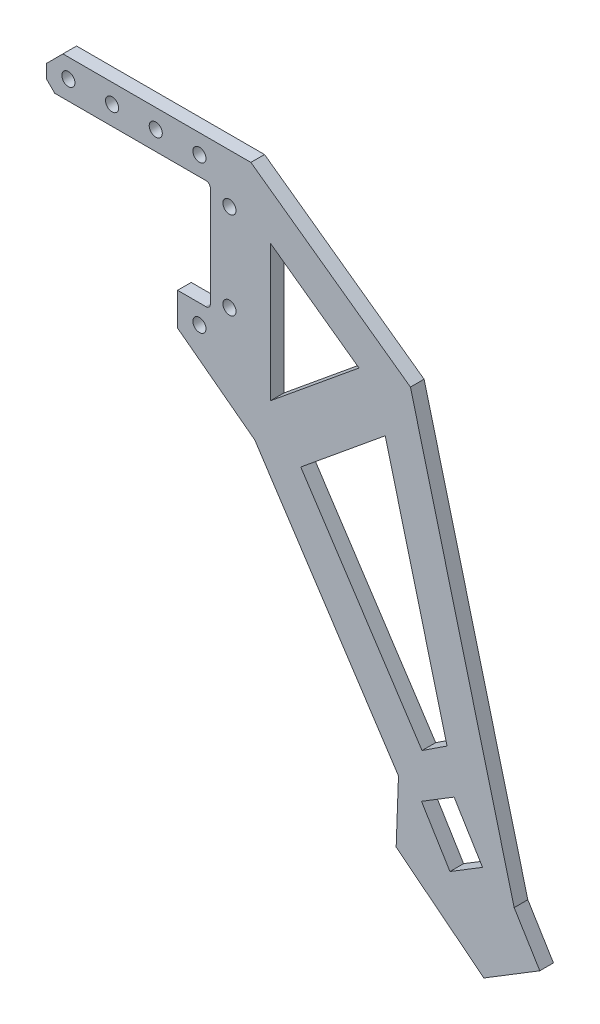
SolidWorks part; units mm, degrees
ref_plane "Plan de face" through (0, 0, 0) normal (0, 0, 1) x (1, 0, 0)
ref_plane "Plan de dessus" through (0, 0, 0) normal (0, 1, 0) x (1, 0, 0)
ref_plane "Plan de droite" through (0, 0, 0) normal (1, 0, 0) x (0, 0, -1)
sketch "Esquisse1" plane through (0, 0, 0) normal (0, 0, 1) x (1, 0, 0)
  line L0 (-12.25, 10) -> (12.25, 10)
  line L1 (19.6775, 17) -> (48.9006, -4.024)
  line L2 (48.9006, -4.024) -> (67.9013, -77.094)
  line L3 (67.9013, -77.094) -> (72.5958, -84.7726)
  line L4 (72.5958, -84.7726) -> (62.3576, -91.032)
  line L5 (62.3576, -91.032) -> (46.2854, -78.3067)
  line L6 (46.2854, -78.3067) -> (46.7112, -66.8067)
  line L7 (46.7112, -66.8067) -> (20.3918, -26.6658)
  line L8 (-12.25, 10) -> (-12.25, -10)
  line L9 (-12.25, -10) -> (12.25, -10)
  line L10 (12.25, 10) -> (12.25, -10)
  line L11 (-17.75, 10) -> (-17.75, -10)
  line L12 (-12.25, 10) -> (12.25, -10) construction
  line L13 (12.25, 10) -> (-12.25, -10) construction
  line L14 (-17.75, 10) -> (-17.75, 17)
  line L15 (-12.25, -10) -> (-17.75, -10)
  line L16 (-12.25, 10) -> (-17.75, 10)
  line L17 (44.278, -14.0621) -> (55.6029, -57.6137)
  line L18 (55.6029, -57.6137) -> (51.0231, -60.6166)
  line L19 (51.0231, -60.6166) -> (28.8161, -26.7478)
  line L20 (28.8161, -26.7478) -> (44.278, -14.0621)
  line L21 (23.25, 5.9738) -> (23.25, -19.0262)
  line L22 (23.25, -19.0262) -> (39.4851, -5.7062)
  line L23 (39.4851, -5.7062) -> (23.25, 5.9738)
  line L24 (19.6775, 17) -> (20.3918, -26.6658)
  line L25 (-1000, 0) -> (49000, 0) construction
  line L26 (-17.75, 17) -> (12.25, 17)
  line L27 (12.25, 17) -> (12.25, 10)
  line L28 (12.25, -10) -> (12.25, -16)
  line L29 (12.25, -16) -> (-17.75, -16)
  line L30 (-17.75, -16) -> (-17.75, -10)
  line L31 (19.6775, 17) -> (12.25, 17)
  line L32 (6.25, -10) -> (6.25, -16)
  line L33 (6.25, -16) -> (20.3918, -26.6658)
  point P17 (10.25, -13.5)
  point P18 (2.25, -13.5)
  point P25 (-5.75, -13.5)
  point P26 (-13.75, -13.5)
  point P27 (10.25, 13.5)
  point P28 (2.25, 13.5)
  point P29 (-5.75, 13.5)
  point P30 (-13.75, 13.5)
  point P31 (15.75, -8)
  point P32 (15.75, 8)
  dimension "D2" = 75.5
  dimension "D3" = 36
  dimension "D4" = 9
  dimension "D5" = 12
  dimension "D6" = 20.5
  dimension "D7" = 11.5
  dimension "D8" = 48
  dimension "D9" = 7
  dimension "D10" = 7
  dimension "D11" = 9.5
  dimension "D12" = 20
  dimension "D13" = 24.5
  dimension "D14" = 8
  dimension "D15" = 27
  dimension "D16" = 3.5
  dimension "D17" = 2
  dimension "D18" = 3.5
  dimension "D19" = 2
  dimension "D20" = 5.5
  dimension "D21" = 8
  dimension "D22" = 8
  dimension "D23" = 8
  dimension "D24" = 8
  dimension "D25" = 8
  dimension "D26" = 16
  dimension "D27" = 6
  dimension "D28" = 7
  dimension "D29" = 4
  dimension "D30" = 11
  dimension "D31" = 20
  dimension "D32" = 40.5
  dimension "D33" = 45
  dimension "D34" = 20
  dimension "D35" = 21
  dimension "D36" = 25
extrude "Boss.-Extru.1" add sketch "Esquisse1" along normal blind 2.5 contours L1 L24 L7 L6 L5 L4 L3 L2 L19 L20 L17 L18 L23 L22 L21 | L29 L33 L24 L31 L27 L10 L28 | L9 L32 L29 L28 | L27 L26 L14 L16 L0
hole_wizard "Dégagement M21" positions "Esquisse3" profile "Esquisse2" hole size "M2" standard "Iso" end condition through all
sketch "Esquisse3" plane through (0, 0, 2.5) normal (0, 0, 1) x (1, 0, 0)
  point P0 (-13.75, 13.5)
  point P3 (-5.75, 13.5)
  point P6 (2.25, 13.5)
  point P9 (10.25, 13.5)
  point P12 (15.75, 8)
  point P15 (15.75, -8)
  point P18 (10.25, -13.5)
sketch "Esquisse2" plane through (-13.75, 13.5, 2.5) normal (1, 0, 0) x (0, -1, 0)
  line L0 (0, 0) -> (0, 2.5)
  line L1 (0, 2.5) -> (1.2, 2.5)
  line L2 (1.2, 2.5) -> (1.2, 0)
  line L5 (1.2, 0) -> (0, 0)
  line L11 (0, -6.35) -> (0, 107.95) construction
  dimension "Diamètre du perçage jusqu'au prochain" = 2.4
  dimension "Profondeur du perçage jusqu'au prochain" = 2.5
chamfer "Chanfrein1" distance 1.5 angle 45 1 edges at (-17.75, 10, 1.25)
chamfer "Chanfrein2" distance 3 distance2 3 1 edges at (-17.75, 17, 1.25)
fillet "Congé3" radius 0.8 2 edges at (12.25, -10, 1.25) (12.25, 10, 1.25)
sketch "Esquisse6" plane through (0, 0, 2.5) normal (0, 0, 1) x (1, 0, 0)
  line L0 (50.9236, -68.7204) -> (56.8959, -65.0691)
  line L1 (50.9236, -68.7204) -> (56.1398, -77.2522)
  line L2 (56.8959, -65.0691) -> (62.112, -73.6009)
  line L3 (56.1398, -77.2522) -> (62.112, -73.6009)
  line L4 (72.5958, -84.7726) -> (62.3576, -91.032) construction
  dimension "D1" = 10
  dimension "D2" = 15
  dimension "D3" = 3.4519
  dimension "D4" = 7
extrude "Enlèv. mat.-Extru.1" cut sketch "Esquisse6" against normal up to next
